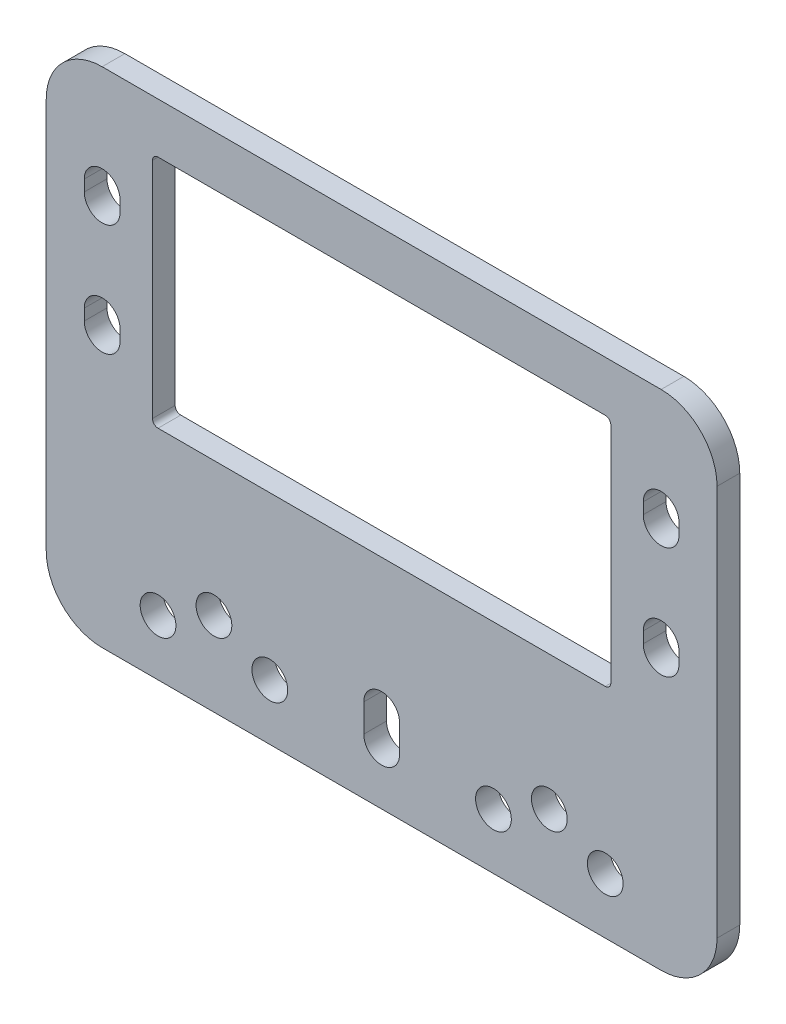
SolidWorks part; units mm, degrees
ref_plane "Front Plane" through (0, 0, 0) normal (0, 0, 1) x (1, 0, 0)
ref_plane "Top Plane" through (0, 0, 0) normal (0, 1, 0) x (1, 0, 0)
ref_plane "Right Plane" through (0, 0, 0) normal (1, 0, 0) x (0, 0, -1)
sketch "Sketch1" plane through (0, 0, 0) normal (0, 0, 1) x (1, 0, 0)
  line L1 (-30, -22.5) -> (30, -22.5)
  line L2 (-30, -22.5) -> (-30, 22.5)
  line L3 (-30, 22.5) -> (30, 22.5)
  line L4 (30, -22.5) -> (30, 22.5)
  line L5 (-30, -22.5) -> (30, 22.5) construction
  line L6 (-30, 22.5) -> (30, -22.5) construction
  point P0 (0, 0)
  dimension "D1" = 60
  dimension "D2" = 45
extrude "Boss-Extrude1" add sketch "Sketch1" along normal blind 2.032
fillet "Fillet1" radius 5 4 edges at (-30, -22.5, 1.016) (30, -22.5, 1.016) (-30, 22.5, 1.016) (30, 22.5, 1.016)
sketch "Sketch2" plane through (0, 0, 2.032) normal (0, 0, 1) x (1, 0, 0)
  line L0 (-41.2577, -7.5) -> (43.7202, -7.5) construction
  line L1 (-25, -22.5) -> (25, -22.5) construction
  line L2 (0, -54.6431) -> (0, 54.6431) construction
  line L3 (-20.5, -3) -> (20.5, -3)
  line L4 (-20.5, -3) -> (-20.5, 18)
  line L5 (-20.5, 18) -> (20.5, 18)
  line L6 (20.5, -3) -> (20.5, 18)
  line L7 (-20.5, -3) -> (20.5, 18) construction
  line L8 (-20.5, 18) -> (20.5, -3) construction
  line L9 (-33.3183, 7.5) -> (35.3128, 7.5) construction
  line L10 (25, 22.5) -> (-25, 22.5) construction
  point P4 (0, 7.5)
  dimension "D1" = 15
  dimension "D2" = 21
  dimension "D3" = 41
extrude "Cut-Extrude1" cut sketch "Sketch2" against normal through all
fillet "Fillet2" radius 0.5 4 edges at (20.5, 18, 1.016) (20.5, -3, 1.016) (-20.5, -3, 1.016) (-20.5, 18, 1.016)
sketch "Sketch3" plane through (0, 0, 2.032) normal (0, 0, 1) x (1, 0, 0)
  line L0 (-25, 3) -> (-25, 2) construction
  line L1 (-23.4, 3) -> (-23.4, 2)
  line L2 (-26.6, 3) -> (-26.6, 2)
  line L3 (-20.5, 7.5) -> (20.5, 7.5) construction
  line L4 (-20.5, 17.5) -> (-20.5, -2.5) construction
  line L5 (20.5, -2.5) -> (20.5, 17.5) construction
  line L6 (0, 18.6557) -> (0, -3.4503) construction
  line L7 (0, -54.6431) -> (0, 54.6431) construction
  line L8 (-25, 12) -> (-25, 13) construction
  line L9 (-23.4, 12) -> (-23.4, 13)
  line L10 (-26.6, 12) -> (-26.6, 13)
  line L11 (25, 3) -> (25, 2) construction
  line L12 (23.4, 3) -> (23.4, 2)
  line L13 (26.6, 3) -> (26.6, 2)
  line L14 (25, 12) -> (25, 13) construction
  line L15 (23.4, 12) -> (23.4, 13)
  line L16 (26.6, 12) -> (26.6, 13)
  arc A0 (-23.4, 3) -> (-26.6, 3) centre (-25, 3) ccw
  arc A1 (-26.6, 2) -> (-23.4, 2) centre (-25, 2) ccw
  arc A2 (-23.4, 12) -> (-26.6, 12) centre (-25, 12) cw
  arc A3 (-26.6, 13) -> (-23.4, 13) centre (-25, 13) cw
  arc A4 (23.4, 3) -> (26.6, 3) centre (25, 3) cw
  arc A5 (26.6, 2) -> (23.4, 2) centre (25, 2) cw
  arc A6 (23.4, 12) -> (26.6, 12) centre (25, 12) ccw
  arc A7 (26.6, 13) -> (23.4, 13) centre (25, 13) ccw
  point P2 (-25, 2.5)
  point P20 (-25, 12.5)
  point P27 (25, 2.5)
  point P34 (25, 12.5)
  dimension "D1" = 10
  dimension "D2" = 50
  dimension "D3" = 3.2
  dimension "D4" = 1
extrude "Cut-Extrude2" cut sketch "Sketch3" against normal through all
sketch "Sketch4" plane through (0, 0, 2.032) normal (0, 0, 1) x (1, 0, 0)
  line L0 (0, -54.6431) -> (0, 54.6431) construction
  line L1 (-30, -15) -> (30, -15) construction
  line L2 (-30, 17.5) -> (-30, -17.5) construction
  line L3 (30, -17.5) -> (30, 17.5) construction
  line L4 (-25, -22.5) -> (25, -22.5) construction
  line L5 (0, 0) -> (0, -6.6395) construction
  line L6 (-30, -17.5) -> (30, -17.5) construction
  line L7 (0, -15) -> (0, -17.5) construction
  line L8 (1.6, -15) -> (1.6, -17.5)
  line L9 (-1.6, -15) -> (-1.6, -17.5)
  circle A0 centre (-15, -15) radius 1.6
  circle A1 centre (0, -15) radius 1.6 construction
  circle A2 centre (15, -15) radius 1.6
  circle A3 centre (-22.5, -15) radius 1.6 construction
  circle A4 centre (-7.5, -15) radius 1.6 construction
  circle A5 centre (7.5, -15) radius 1.6 construction
  circle A6 centre (22.5, -15) radius 1.6 construction
  circle A7 centre (0, -17.5) radius 1.6 construction
  circle A8 centre (10, -17.5) radius 1.6
  circle A9 centre (-10, -17.5) radius 1.6
  circle A10 centre (20, -17.5) radius 1.6
  circle A11 centre (-20, -17.5) radius 1.6
  arc A12 (1.6, -15) -> (-1.6, -15) centre (0, -15) ccw
  arc A13 (-1.6, -17.5) -> (1.6, -17.5) centre (0, -17.5) ccw
  point P39 (0, -16.25)
  dimension "D1" = 3.2
  dimension "D2" = 7.5
  dimension "D3" = 15
  dimension "D4" = 15
  dimension "D5" = 15
  dimension "D6" = 7.5
  dimension "D7" = 5
  dimension "D8" = 10
  dimension "D9" = 10
  dimension "D10" = 10
extrude "Cut-Extrude3" cut sketch "Sketch4" against normal through all
